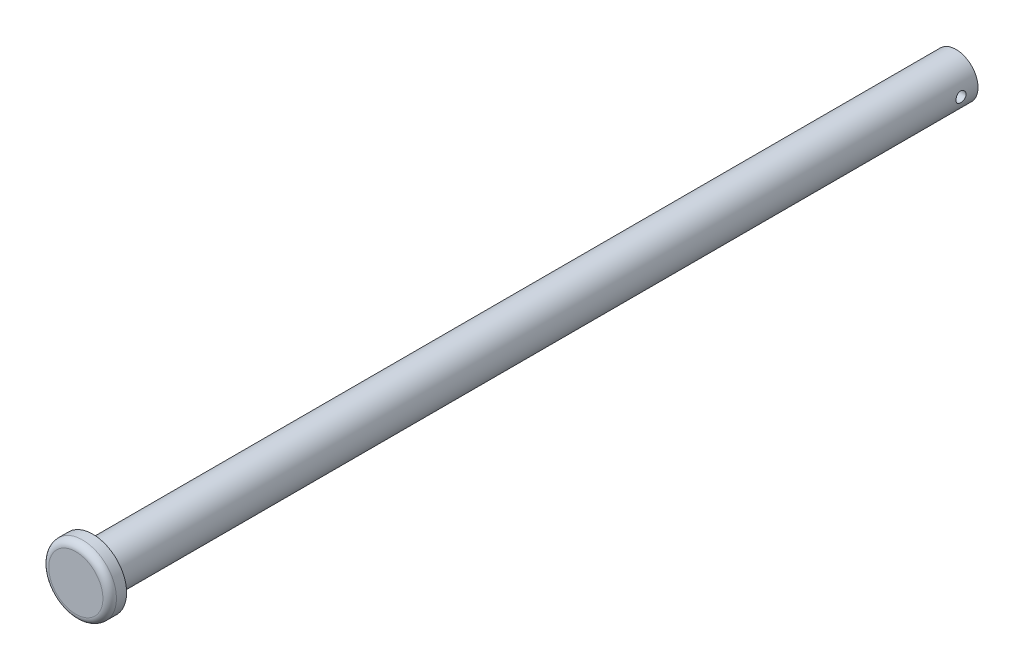
SolidWorks part; units mm, degrees
ref_plane "Front Plane" through (0, 0, 0) normal (0, 0, 1) x (1, 0, 0)
ref_plane "Top Plane" through (0, 0, 0) normal (0, 1, 0) x (1, 0, 0)
ref_plane "Right Plane" through (0, 0, 0) normal (1, 0, 0) x (0, 0, -1)
sketch "Sketch1" plane through (0, 0, 0) normal (0, 0, 1) x (1, 0, 0)
  circle A0 centre (0, 0) radius 6.5
  dimension "D1" = 13
extrude "Boss-Extrude1" add sketch "Sketch1" along normal blind 255
sketch "Sketch2" plane through (0, 0, 255) normal (0, 0, 1) x (1, 0, 0)
  circle A0 centre (0, 0) radius 10
  dimension "D1" = 20
extrude "Boss-Extrude2" add sketch "Sketch2" along normal blind 5
fillet "Fillet1" radius 2 2 edges at (10, 0, 260) (6.5, 0, 255)
sketch "Sketch3" plane through (0, 0, 0) normal (1, 0, 0) x (0, 0, -1)
  circle A0 centre (-5, 0) radius 1.5
  dimension "D2" = 3
  dimension "D1" = 5
extrude "Cut-Extrude1" cut sketch "Sketch3" against normal through all both and the other way through all
